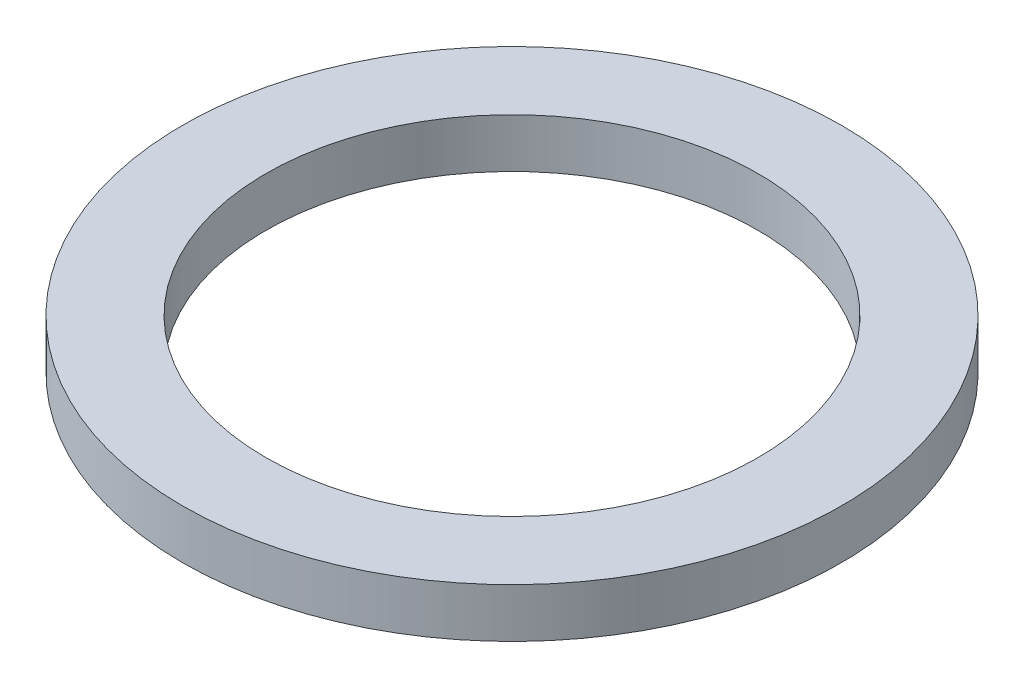
SolidWorks part; units mm, degrees
ref_plane "Front Plane" through (0, 0, 0) normal (0, 0, 1) x (1, 0, 0)
ref_plane "Top Plane" through (0, 0, 0) normal (0, 1, 0) x (1, 0, 0)
ref_plane "Right Plane" through (0, 0, 0) normal (1, 0, 0) x (0, 0, -1)
sketch "Sketch1" plane through (0, 0, 0) normal (0, 1, 0) x (1, 0, 0)
  circle A0 centre (0, 0) radius 4.7625
  dimension "OD" = 9.525
extrude "Boss-Extrude1" add sketch "Sketch1" along normal blind 0.7112
sketch "Sketch5" plane through (0, 0.7112, 0) normal (0, 1, 0) x (-1, 0, 0)
  circle A0 centre (0, 0) radius 3.556
  dimension "ID" = 7.112
extrude "Cut-Extrude1" cut sketch "Sketch5" against normal through all
